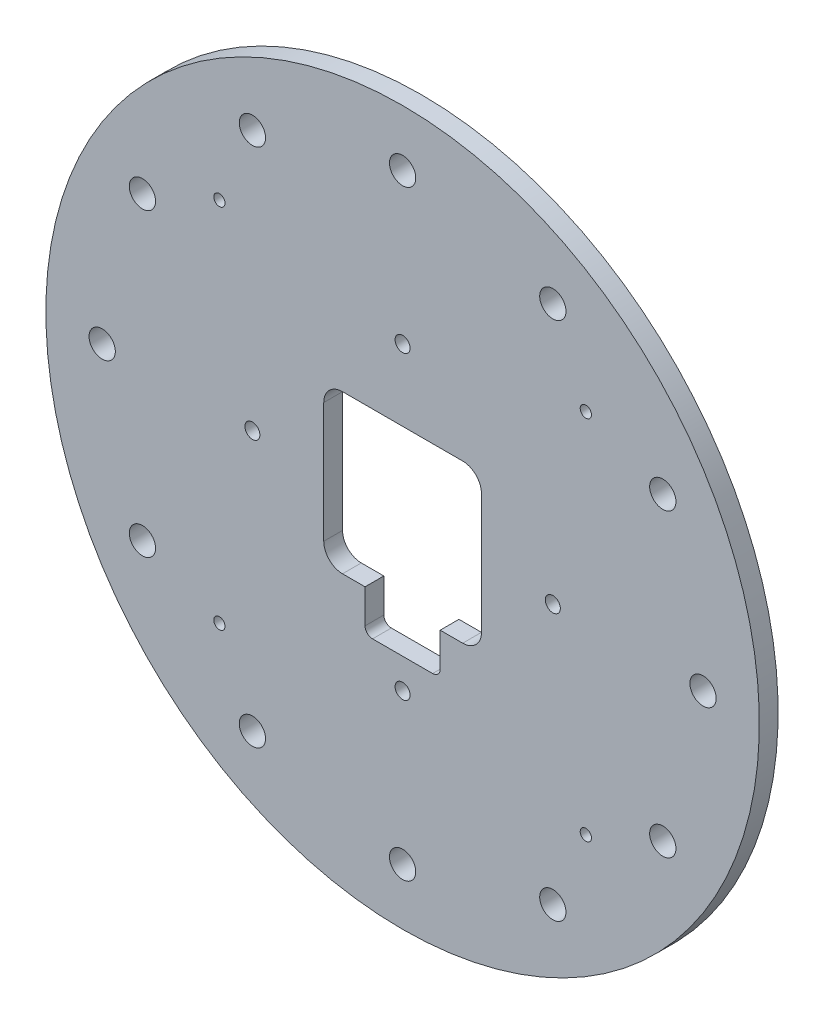
SolidWorks part; units mm, degrees
ref_plane "Front Plane" through (0, 0, 0) normal (0, 0, 1) x (1, 0, 0)
ref_plane "Top Plane" through (0, 0, 0) normal (0, 1, 0) x (1, 0, 0)
ref_plane "Right Plane" through (0, 0, 0) normal (1, 0, 0) x (0, 0, -1)
sketch "Sketch1" plane through (0, 0, 0) normal (0, 1, 0) x (1, 0, 0)
  line L0 (0, 0) -> (69, 0) construction
  line L1 (0, 0) -> (48.7904, 48.7904) construction
  line L2 (10, -21) -> (10, -30.0001)
  line L3 (-16.0057, -21) -> (-10, -21)
  line L4 (-21, -16) -> (-21, 16)
  line L5 (-16, 21) -> (16, 21)
  line L6 (21.0004, -16.0016) -> (21.0004, 16.0016)
  line L7 (0, 21) -> (0, -21) construction
  line L8 (-21, 0) -> (21.0004, 0) construction
  line L9 (8, -32.0001) -> (-8.0002, -32.0001)
  line L10 (-10, -30.0001) -> (-10, -21)
  line L11 (10, -21) -> (16.0019, -21)
  line L12 (0, 0) -> (0, 40) construction
  line L13 (69, 0) -> (80, 0) construction
  circle A6 centre (0, 0) radius 69 construction
  circle A8 centre (48.7904, 48.7904) radius 1.5
  circle A21 centre (0, 0) radius 40 construction
  circle A22 centre (0, 40) radius 2
  circle A23 centre (0, 0) radius 40 construction
  circle A24 centre (40, 0) radius 2
  circle A25 centre (0, 0) radius 40 construction
  circle A26 centre (0, -40) radius 2
  circle A27 centre (0, 0) radius 40 construction
  circle A28 centre (-40, 0) radius 2
  arc A29 (-21, 16) -> (-16, 21) centre (-16, 16) cw
  arc A30 (21.0004, 16.0016) -> (16, 21) centre (16.001, 16.0006) ccw
  arc A31 (-21, -16) -> (-16.0057, -21) centre (-16.0029, -16.0029) ccw
  arc A32 (21.0004, -16.0016) -> (16.0019, -21) centre (16.0019, -16.0016) cw
  arc A33 (-10, -30.0001) -> (-8.0002, -32.0001) centre (-8.0001, -30.0002) ccw
  arc A34 (10, -30.0001) -> (8, -32.0001) centre (8, -30.0001) cw
  circle A42 centre (0, 0) radius 69 construction
  circle A43 centre (48.7904, -48.7904) radius 1.5
  circle A44 centre (0, 0) radius 69 construction
  circle A48 centre (-48.7904, -48.7904) radius 1.5
  circle A49 centre (0, 0) radius 69 construction
  circle A52 centre (-48.7904, 48.7904) radius 1.5
  circle A53 centre (0, 0) radius 95
  circle A55 centre (0, 0) radius 80 construction
  circle A61 centre (80, 0) radius 3.5
  circle A62 centre (0, 0) radius 80 construction
  circle A63 centre (69.282, -40) radius 3.5
  circle A64 centre (0, 0) radius 80 construction
  circle A65 centre (40, -69.282) radius 3.5
  circle A66 centre (0, 0) radius 80 construction
  circle A67 centre (0, -80) radius 3.5
  circle A68 centre (0, 0) radius 80 construction
  circle A69 centre (-40, -69.282) radius 3.5
  circle A70 centre (0, 0) radius 80 construction
  circle A71 centre (-69.282, -40) radius 3.5
  circle A72 centre (0, 0) radius 80 construction
  circle A73 centre (-80, 0) radius 3.5
  circle A74 centre (0, 0) radius 80 construction
  circle A75 centre (-69.282, 40) radius 3.5
  circle A76 centre (0, 0) radius 80 construction
  circle A77 centre (-40, 69.282) radius 3.5
  circle A78 centre (0, 0) radius 80 construction
  circle A79 centre (0, 80) radius 3.5
  circle A80 centre (0, 0) radius 80 construction
  circle A81 centre (40, 69.282) radius 3.5
  circle A82 centre (0, 0) radius 80 construction
  circle A83 centre (69.282, 40) radius 3.5
  point P18 (0, 0)
  point P24 (0, 0)
  point P40 (0, 0)
  point P64 (0, 0)
  point P90 (0, 0)
  point P91 (0, 0)
  point P99 (0, 0)
  dimension "D4" = 138
  dimension "D5" = 45
  dimension "D6" = 42
  dimension "D15" = 80
  dimension "D16" = 4
  dimension "D18" = 90
  dimension "D19" = 5
  dimension "D20" = 90
  dimension "D21" = 4.9994
  dimension "D22" = 90
  dimension "D23" = 4.9971
  dimension "D24" = 90
  dimension "D25" = 4.9984
  dimension "D26" = 90
  dimension "D27" = 1.9999
  dimension "D28" = 90
  dimension "D29" = 2
  dimension "D10" = 160
  dimension "D7" = 3
  dimension "D8" = 4
  dimension "D9" = 190
  dimension "D11" = 7
  dimension "D12" = 20
  dimension "D13" = 6.0019
  dimension "D14" = 42.0004
  dimension "D17" = 4
  dimension "D30" = 16.0001
  dimension "D31" = 42
  dimension "D32" = 32
  dimension "D33" = 32.0077
  dimension "D34" = 12
  dimension "D35" = 32
  dimension "D36" = 20
  dimension "D37" = 30.0002
extrude "Boss-Extrude1" add sketch "Sketch1" along normal blind 5
move or copy body "Body-Move/Copy1" bodies to move or copy 101 copy no rotation origin (0, 2.5, 0) rotation axis (1, 0, 0) rotation angle 90
